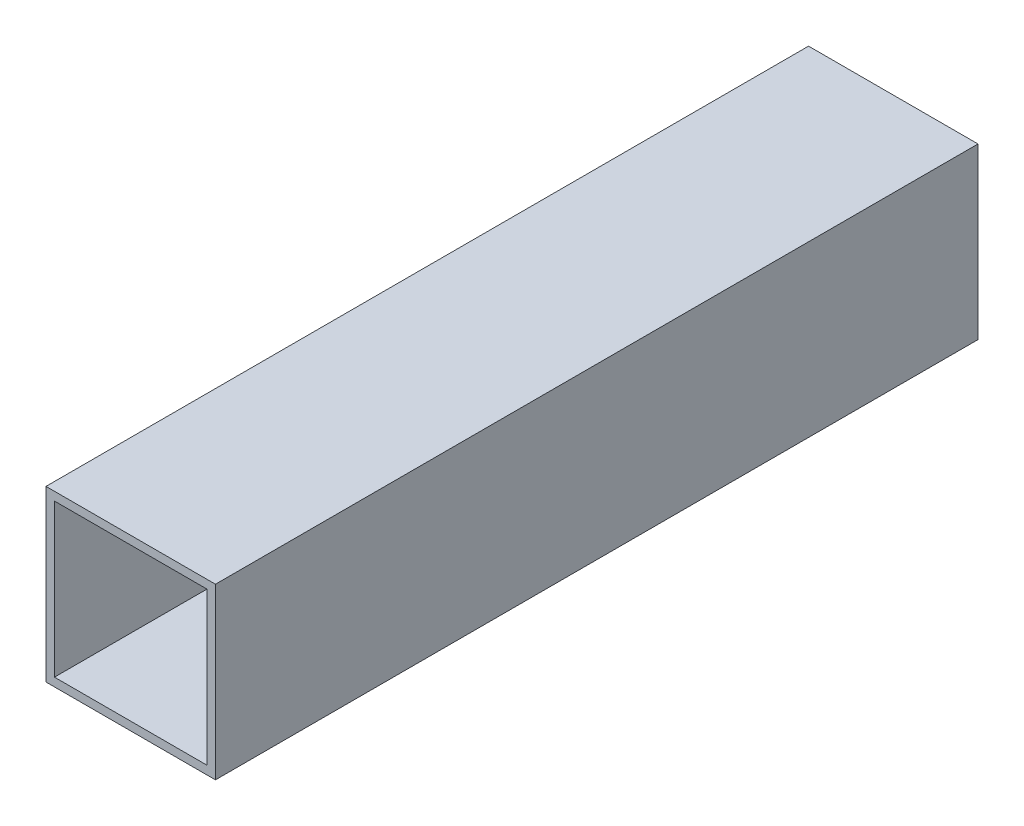
SolidWorks part; units mm, degrees
material "Plain Carbon Steel"
ref_plane "Front Plane" through (0, 0, 0) normal (0, 0, 1) x (1, 0, 0)
ref_plane "Top Plane" through (0, 0, 0) normal (0, 1, 0) x (1, 0, 0)
ref_plane "Right Plane" through (0, 0, 0) normal (1, 0, 0) x (0, 0, -1)
sketch "Sketch1" plane through (0, 0, 0) normal (0, 0, 1) x (1, 0, 0)
  line B0 (-50, -50) -> (50, -50)
  line B1 (-50, -50) -> (-50, 50)
  line B2 (50, -50) -> (50, 50)
  line B3 (-50, 50) -> (50, 50)
  line B4 (-45, -45) -> (45, -45)
  line B5 (-45, -45) -> (-45, 45)
  line B6 (45, -45) -> (45, 45)
  line B7 (-45, 45) -> (45, 45)
sketch_block_instance "10x10x5_profil-1"
sketch_block "10x10x5_profil" parameters "D1"=100, "D2"=100, "D3"=5, "D4"=5
extrude "Boss-Extrude1" add sketch "Sketch1" along normal mid plane 450
